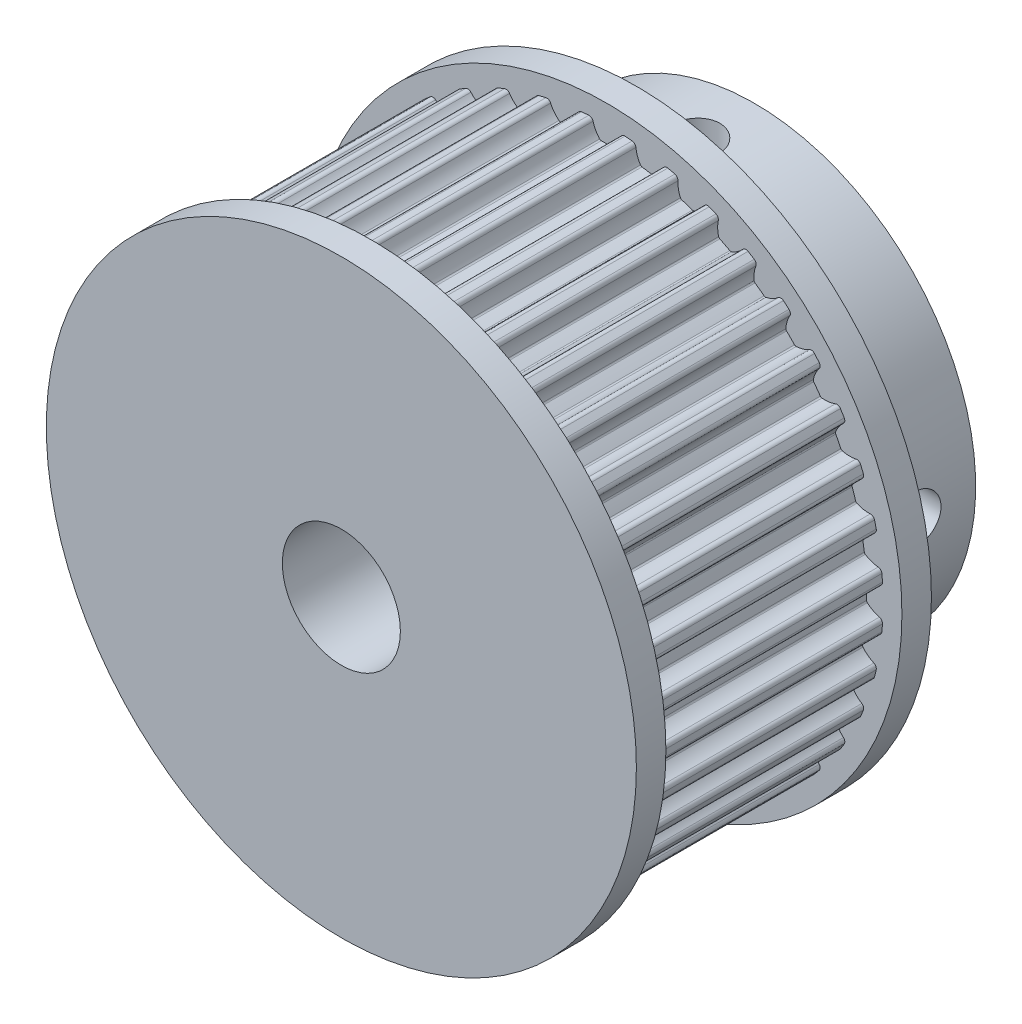
SolidWorks part; units mm, degrees
material "6061-T6 (SS)"
ref_plane "前基準面" through (0, 0, 0) normal (0, 0, 1) x (1, 0, 0)
ref_plane "上基準面" through (0, 0, 0) normal (0, 1, 0) x (1, 0, 0)
ref_plane "右基準面" through (0, 0, 0) normal (1, 0, 0) x (0, 0, -1)
sketch "草圖1" plane through (0, 0, 0) normal (0, 0, 1) x (1, 0, 0)
  circle A0 centre (0, 0) radius 18.72
  dimension "D1" = 37.44
extrude "填料-伸長1" add sketch "草圖1" along normal mid plane 16
sketch "草圖2" plane through (0, 0, 8) normal (0, 0, 1) x (1, 0, 0)
  line L0 (0, 0) -> (0, 18.974) construction
  line L1 (-0.975, 18.974) -> (0.975, 18.974) construction
  arc A0 (-0.3807, 17.6059) -> (0.3807, 17.6059) centre (0, 0) cw
  circle A1 centre (0, 0) radius 18.72 construction
  arc A2 (-1.2242, 18.6799) -> (-0.9351, 18.4717) centre (-1.2059, 18.4005) cw
  arc A3 (-0.9351, 18.4717) -> (-0.4956, 17.6557) centre (0.975, 18.974) ccw
  arc A4 (-0.4956, 17.6557) -> (-0.3807, 17.6059) centre (-0.3839, 17.7558) ccw
  arc A5 (0.4956, 17.6557) -> (0.3807, 17.6059) centre (0.3839, 17.7558) cw
  arc A6 (0.9351, 18.4717) -> (0.4956, 17.6557) centre (-0.975, 18.974) cw
  arc A7 (1.2242, 18.6799) -> (0.9351, 18.4717) centre (1.2059, 18.4005) ccw
  point P6 (0, 17.61)
  point P18 (0, 18.72)
  dimension "D1" = 1.11
  dimension "D2" = 0.15
  dimension "D3" = 1.975
  dimension "D4" = 0.28
  dimension "D5" = 1.95
  dimension "D6" = 0.254
extrude "除料-伸長1" cut sketch "草圖2" against normal through all and the other way through all flip side to cut
pattern_circular "環狀複製排列1" count 40 over 360 about axis through (0, 0, 8) along (0, 0, 1) of "除料-伸長1"
sketch "草圖3" plane through (0, 0, 8) normal (0, 0, 1) x (1, 0, 0)
  circle A0 centre (0, 0) radius 20
  dimension "D1" = 40
extrude "填料-伸長2" add sketch "草圖3" along normal blind 2
mirror "鏡射1" about plane through (0, 0, 0) normal (0, 0, 1) of "填料-伸長2"
sketch "草圖5" plane through (0, 0, -10) normal (0, 0, -1) x (-1, 0, 0)
  circle A0 centre (0, 0) radius 15
  dimension "D1" = 30
extrude "填料-伸長3" add sketch "草圖5" along normal blind 8
sketch "草圖4" plane through (0, 0, 10) normal (0, 0, 1) x (1, 0, 0)
  circle A0 centre (0, 0) radius 4
  dimension "D1" = 8
extrude "除料-伸長2" cut sketch "草圖4" against normal through all
hole_wizard "M4x0.7 螺紋孔1" positions "草圖6" profile "草圖7" tap size "M4x0.7" standard "Ansi Metric"
sketch "草圖6" plane through (0, 0, 0) normal (0, 1, 0) x (1, 0, 0)
  line L3 (0, 18) -> (0, 10) construction
  line L4 (4, 18) -> (-4, 18) construction
  line L5 (20, 10) -> (-20, 10) construction
  point P11 (0, 14)
  point P23 (0, 0)
sketch "草圖7" plane through (0, 0, -14) normal (1, 0, 0) x (0, 0, -1)
  line L0 (0, 0) -> (0, 20)
  line L1 (0, 20) -> (1.65, 20)
  line L2 (1.65, 20) -> (1.65, 0)
  line L5 (1.65, 0) -> (0, 0)
  line L11 (0, -6.35) -> (0, 107.95) construction
  dimension "貫穿螺孔鑽直徑" = 3.3
  dimension "貫穿螺孔鑽深度" = 20
pattern_circular "環狀複製排列2" count 2 every 90 about axis through (0, 0, -18) along (0, 0, -1) of "M4x0.7 螺紋孔1"
